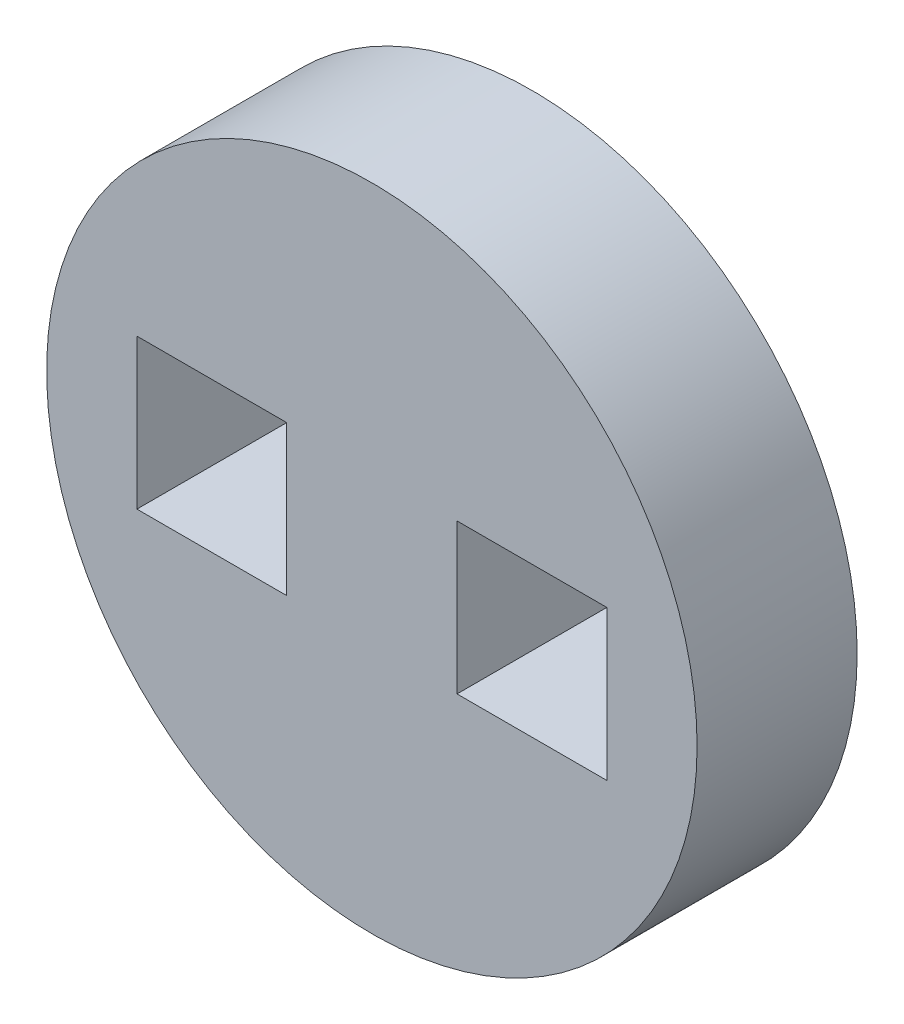
SolidWorks part; units mm, degrees
ref_plane "Front Plane" through (0, 0, 0) normal (0, 0, 1) x (1, 0, 0)
ref_plane "Top Plane" through (0, 0, 0) normal (0, 1, 0) x (1, 0, 0)
ref_plane "Right Plane" through (0, 0, 0) normal (1, 0, 0) x (0, 0, -1)
sketch "Sketch1" plane through (0, 0, 0) normal (0, 0, 1) x (1, 0, 0)
  line L0 (-4.6609, -1.4859) -> (-4.6609, 1.4859)
  line L1 (1.5875, -1.5875) -> (4.7625, -1.5875) construction
  line L2 (1.5875, -1.5875) -> (1.5875, 1.5875) construction
  line L3 (1.5875, 1.5875) -> (4.7625, 1.5875) construction
  line L4 (4.7625, -1.5875) -> (4.7625, 1.5875) construction
  line L5 (1.5875, -1.5875) -> (4.7625, 1.5875) construction
  line L6 (1.5875, 1.5875) -> (4.7625, -1.5875) construction
  line L7 (-4.7625, -1.5875) -> (-1.5875, -1.5875) construction
  line L8 (-4.7625, -1.5875) -> (-4.7625, 1.5875) construction
  line L9 (-4.7625, 1.5875) -> (-1.5875, 1.5875) construction
  line L10 (-1.5875, -1.5875) -> (-1.5875, 1.5875) construction
  line L11 (-4.7625, -1.5875) -> (-1.5875, 1.5875) construction
  line L12 (-4.7625, 1.5875) -> (-1.5875, -1.5875) construction
  line L13 (-4.6609, 1.4859) -> (-1.6891, 1.4859)
  line L14 (-1.6891, -1.4859) -> (-1.6891, 1.4859)
  line L15 (-4.6609, -1.4859) -> (-1.6891, -1.4859)
  line L16 (1.6891, -1.4859) -> (1.6891, 1.4859)
  line L17 (1.6891, 1.4859) -> (4.6609, 1.4859)
  line L18 (4.6609, -1.4859) -> (4.6609, 1.4859)
  line L19 (1.6891, -1.4859) -> (4.6609, -1.4859)
  circle A0 centre (0, 0) radius 6.35 construction
  circle A1 centre (0, 0) radius 6.4516
  point P3 (3.175, 0)
  point P8 (-3.175, 0)
  dimension "D1" = 12.7
  dimension "D2" = 3.175
  dimension "D3" = 3.175
  dimension "D4" = 3.175
  dimension "D5" = 0.1016
  dimension "D6" = 0.1016
extrude "Boss-Extrude1" add sketch "Sketch1" along normal blind 3.175
